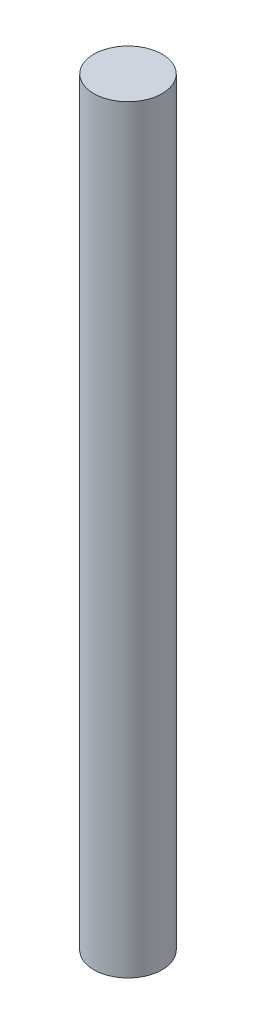
SolidWorks part; units mm, degrees
ref_plane "Alzado" through (0, 0, 0) normal (0, 0, 1) x (1, 0, 0)
ref_plane "Planta" through (0, 0, 0) normal (0, 1, 0) x (1, 0, 0)
ref_plane "Vista lateral" through (0, 0, 0) normal (1, 0, 0) x (0, 0, -1)
sketch "Croquis1" plane through (0, 0, 0) normal (0, 1, 0) x (1, 0, 0)
  circle A0 centre (0, 0) radius 4.5
  dimension "D1" = 9
extrude "Saliente-Extruir1" add sketch "Croquis1" along normal blind 100
